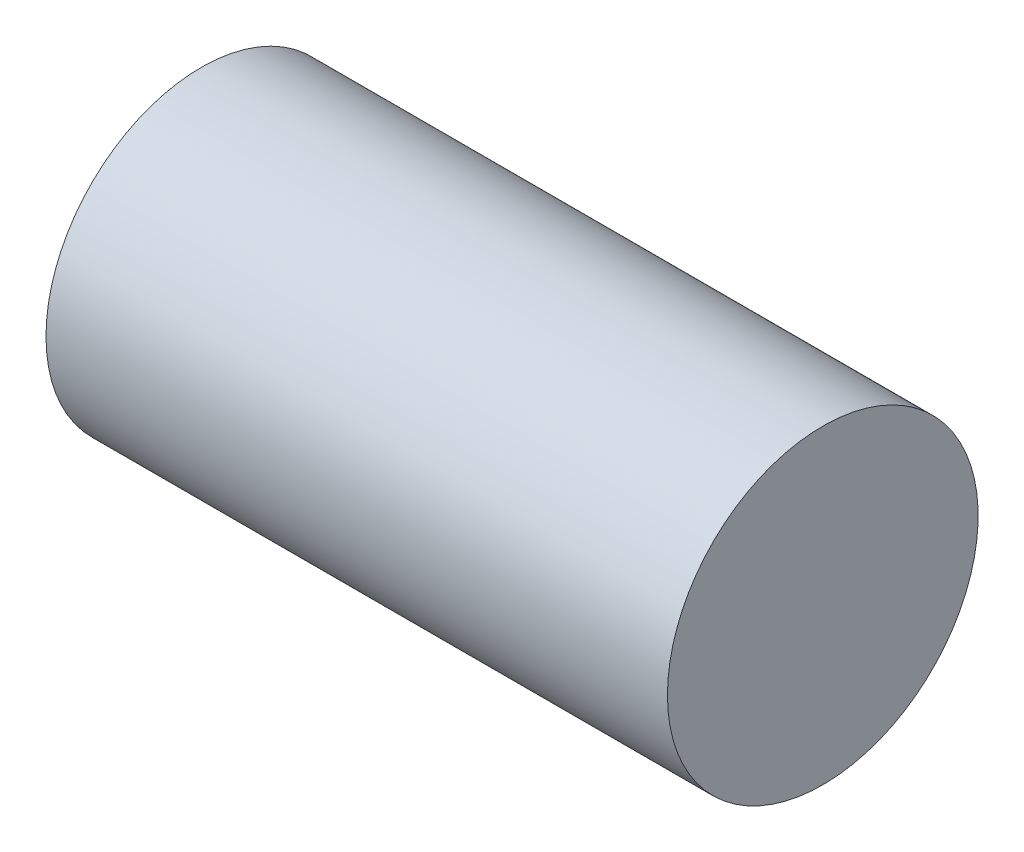
SolidWorks part; units mm, degrees
material "1023 al carbonio, lamiera (SS)"
ref_plane "Piano frontale" through (0, 0, 0) normal (0, 0, 1) x (1, 0, 0)
ref_plane "Piano superiore" through (0, 0, 0) normal (0, 1, 0) x (1, 0, 0)
ref_plane "Piano destro" through (0, 0, 0) normal (1, 0, 0) x (0, 0, -1)
sketch "Schizzo1" plane through (0, 0, 0) normal (0, 0, 1) x (1, 0, 0)
  line L1 (0, 0) -> (40, 0)
  line L2 (0, 0) -> (0, 10)
  line L3 (0, 10) -> (40, 10)
  line L4 (40, 0) -> (40, 10)
  dimension "D1" = 10
  dimension "D2" = 40
revolve "Rivoluzione1" add sketch "Schizzo1" angle 360 about L3
